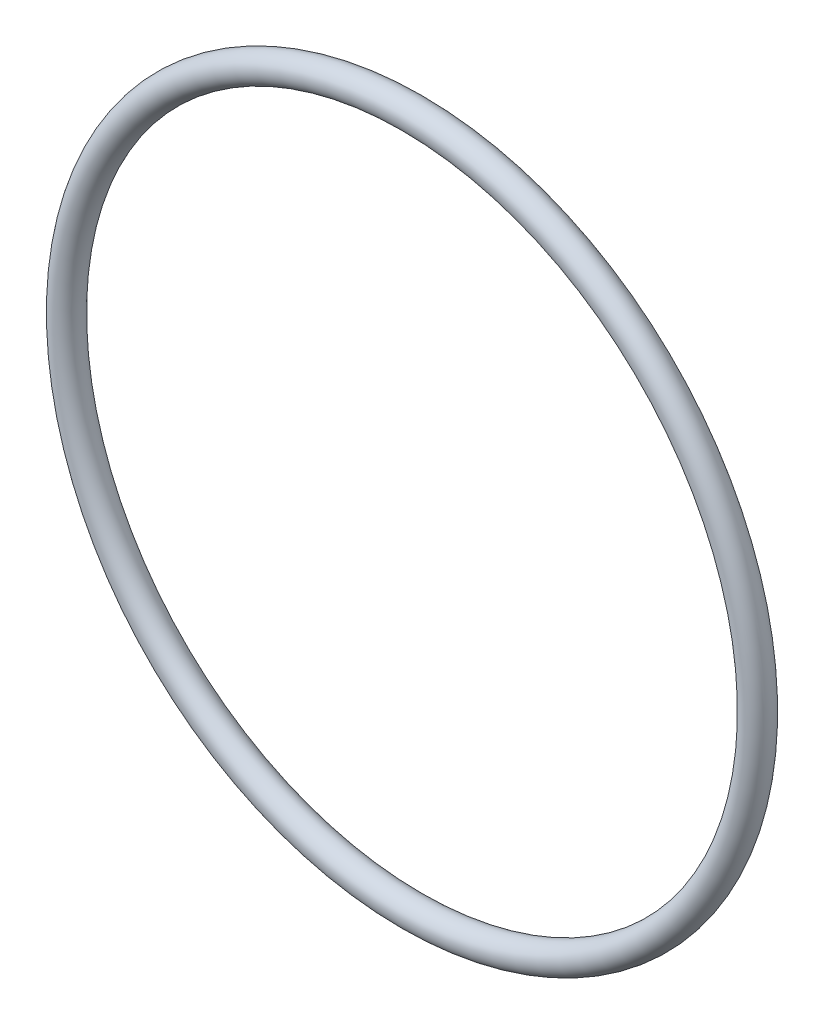
SolidWorks part; units mm, degrees
ref_plane "Front Plane" through (0, 0, 0) normal (0, 0, 1) x (1, 0, 0)
ref_plane "Top Plane" through (0, 0, 0) normal (0, 1, 0) x (1, 0, 0)
ref_plane "Right Plane" through (0, 0, 0) normal (1, 0, 0) x (0, 0, -1)
sketch "Sketch1" plane through (0, 0, 0) normal (0, 0, 1) x (1, 0, 0)
  circle A0 centre (0, 0) radius 60.75
sketch "Sketch2" plane through (0, 0, 0) normal (1, 0, 0) x (0, 0, -1)
  line L0 (0, 60.75) -> (0, -60.75) construction
  circle A0 centre (0, 60.75) radius 2.5
  point P4 (0, 0)
sweep "Sweep1" add profiles "Sketch2" path "Sketch1"
